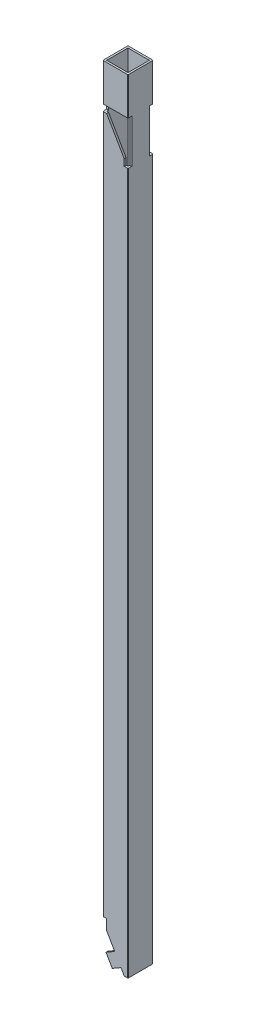
SolidWorks part; units mm, degrees
ref_plane "Front Plane" through (0, 0, 0) normal (0, 0, 1) x (1, 0, 0)
ref_plane "Top Plane" through (0, 0, 0) normal (0, 1, 0) x (1, 0, 0)
ref_plane "Right Plane" through (0, 0, 0) normal (1, 0, 0) x (0, 0, -1)
sketch "Sketch1" plane through (0, 0, 0) normal (0, 1, 0) x (1, 0, 0)
  line L0 (1.5, 1.5) -> (18.5, 1.5)
  line L1 (0.5, 0) -> (19.5, 0)
  line L2 (0, 0.5) -> (0, 19.5)
  line L3 (0.5, 20) -> (19.5, 20)
  line L4 (20, 0.5) -> (20, 19.5)
  line L5 (18.5, 1.5) -> (18.5, 18.5)
  line L6 (1.5, 18.5) -> (18.5, 18.5)
  line L7 (1.5, 1.5) -> (1.5, 18.5)
  arc A0 (19.5, 0) -> (20, 0.5) centre (19.5, 0.5) ccw
  arc A1 (0.5, 0) -> (0, 0.5) centre (0.5, 0.5) cw
  arc A2 (0, 19.5) -> (0.5, 20) centre (0.5, 19.5) cw
  arc A3 (19.5, 20) -> (20, 19.5) centre (19.5, 19.5) cw
  arc A4 (18.5, 1.5) -> (18.5, 1.5) centre (18.5, 1.5) ccw
  arc A5 (18.5, 18.5) -> (18.5, 18.5) centre (18.5, 18.5) cw
  arc A6 (1.5, 18.5) -> (1.5, 18.5) centre (1.5, 18.5) cw
  arc A7 (1.5, 1.5) -> (1.5, 1.5) centre (1.5, 1.5) cw
  point P9 (0, 0)
  dimension "D3" = 0.5
  dimension "D1" = 20
  dimension "D2" = 20
  dimension "D4" = 1.5
extrude "Boss-Extrude1" add sketch "Sketch1" along normal blind 625
sketch "Sketch2" plane through (0, 0, 0) normal (0, 0, 1) x (1, 0, 0)
  line L0 (9.4047, 15.1554) -> (3, 26.2487)
  line L1 (0, 625) -> (0, 0) construction
  line L2 (0, 34.641) -> (0, 0)
  line L3 (0, 0) -> (20, 0)
  line L4 (14.4047, 6.4952) -> (7.4765, 2.4952)
  line L5 (7.4765, 2.4952) -> (2.4765, 11.1554)
  line L6 (2.4765, 11.1554) -> (9.4047, 15.1554)
  line L7 (14.4047, 6.4952) -> (17, 2)
  line L8 (17, 2) -> (20, 2)
  line L9 (20, 625) -> (20, 0) construction
  line L10 (20, 2) -> (20, 0)
  line L11 (3, 26.2487) -> (3, 34.641)
  line L12 (3, 34.641) -> (0, 34.641)
  line L13 (14.4047, 6.4952) -> (18.1547, 0) construction
  dimension "D1" = 60
  dimension "D2" = 10
  dimension "D3" = 8
  dimension "D4" = 7.5
  dimension "D5" = 3
  dimension "D6" = 3
  dimension "D7" = 2
extrude "Cut-Extrude1" cut sketch "Sketch2" against normal through all
sketch "Sketch4" plane through (0, 0, 0) normal (0, 0, 1) x (1, 0, 0)
  line L0 (20, 595) -> (20, 560.359)
  line L1 (20, 625) -> (20, 2) construction
  line L2 (17, 565.5551) -> (3, 589.8038)
  line L3 (0, 625) -> (0, 34.641) construction
  line L4 (0, 595) -> (20, 595)
  line L5 (0.5, 625) -> (19.5, 625) construction
  line L6 (3, 589.8038) -> (0, 589.8038)
  line L7 (0, 589.8038) -> (0, 595)
  line L8 (20, 560.359) -> (17, 560.359)
  line L9 (17, 560.359) -> (17, 565.5551)
  dimension "D1" = 60
  dimension "D2" = 30
  dimension "D3" = 3
  dimension "D4" = 3
extrude "Cut-Extrude9" cut sketch "Sketch4" against normal blind 3
ref_plane "Plane1" through (0, 0, -10) normal (0, 0, 1) x (1, 0, 0)
mirror "Mirror2" about plane through (0, 0, -10) normal (0, 0, 1) of "Cut-Extrude9"
